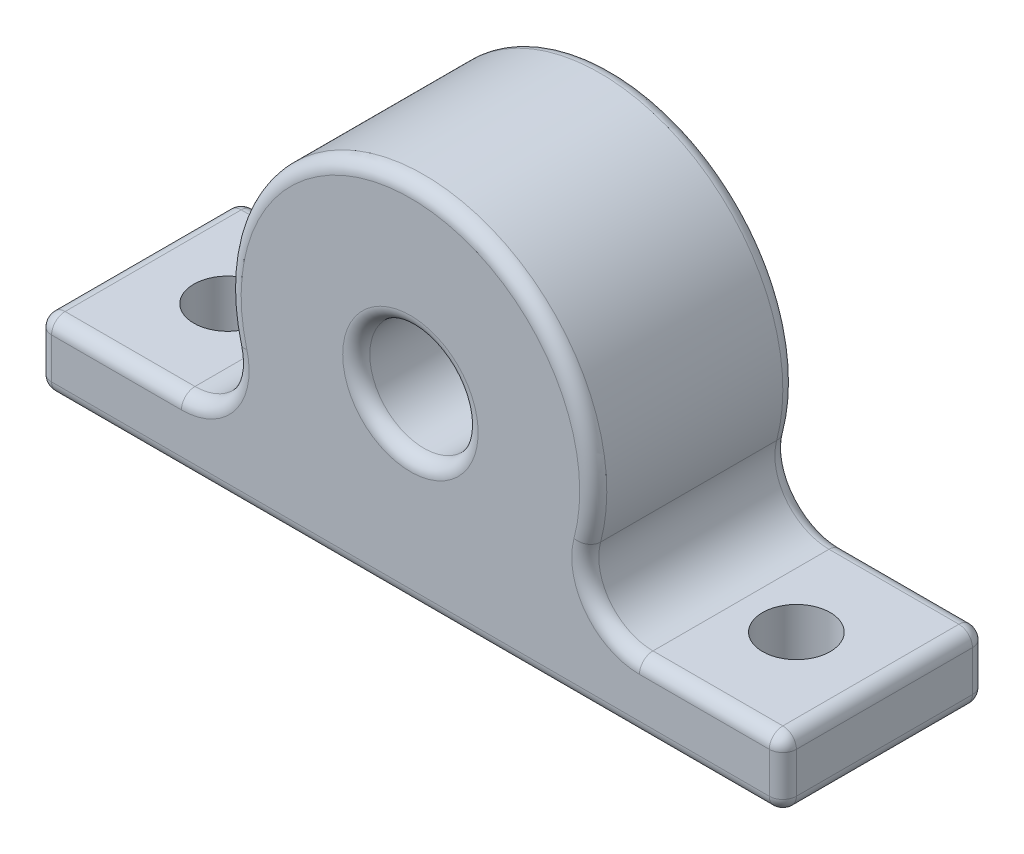
SolidWorks part; units mm, degrees
ref_plane "Piano frontale" through (0, 0, 0) normal (0, 0, 1) x (1, 0, 0)
ref_plane "Piano superiore" through (0, 0, 0) normal (0, 1, 0) x (1, 0, 0)
ref_plane "Piano destro" through (0, 0, 0) normal (1, 0, 0) x (0, 0, -1)
sketch "Schizzo1" plane through (0, 0, 0) normal (0, 1, 0) x (1, 0, 0)
  line L1 (-27.5, 7.5) -> (27.5, 7.5)
  line L2 (-27.5, 7.5) -> (-27.5, -7.5)
  line L3 (-27.5, -7.5) -> (27.5, -7.5)
  line L4 (27.5, 7.5) -> (27.5, -7.5)
  line L5 (-27.5, 7.5) -> (27.5, -7.5) construction
  line L6 (-27.5, -7.5) -> (27.5, 7.5) construction
  point P0 (0, 0)
  dimension "D1" = 15
  dimension "D2" = 55
extrude "Estrusione-Estrusione1" add sketch "Schizzo1" along normal blind 5
sketch "Schizzo2" plane through (0, 0, 0) normal (0, 0, 1) x (1, 0, 0)
  line L1 (5.5, 0) -> (-5.5, 0) construction
  line L2 (0, -5.5) -> (0, 5.5) construction
  circle A0 centre (0, 13.5) radius 13.5
  circle A1 centre (0, 13.5) radius 4
  point P4 (0, 0)
  dimension "D1" = 27
  dimension "D2" = 8
extrude "Estrusione-Estrusione2" add sketch "Schizzo2" along normal up to surface and the other way up to surface up to face at (0, 2.5, 7.5) other way up to face at (0, 2.5, -7.5)
fillet "Raccordo1" radius 4 2 edges at (10.4881, 5, 0) (-10.4881, 5, 0)
fillet "Raccordo2" radius 1 22 edges at (27.5, 5, 0) (27.5, 0, 0) (-27.5, 5, 0) (-27.5, 0, 0) (4, 13.5, -7.5) (-27.5, 2.5, -7.5) (0, 0, -7.5) (27.5, 2.5, -7.5) (22.2058, 5, -7.5) (13.7402, 6.5622, -7.5) (0, 27, -7.5) (-13.7402, 6.5622, -7.5) (-22.2058, 5, -7.5) (-4, 13.5, 7.5) (27.5, 2.5, 7.5) (0, 0, 7.5) (-27.5, 2.5, 7.5) (-22.2058, 5, 7.5) (-13.7402, 6.5622, 7.5) (0, 27, 7.5) (13.7402, 6.5622, 7.5) (22.2058, 5, 7.5)
sketch "Schizzo3" plane through (0, 0, 0) normal (0, 1, 0) x (1, 0, 0)
  line L0 (-23.5, 0) -> (23.5, 0) construction
  line L2 (0, -5.5) -> (0, 5.5) construction
  circle A0 centre (21, 0) radius 2.5
  circle A1 centre (-21, 0) radius 2.5
  point P2 (0, 0)
  dimension "D2" = 5
  dimension "D1" = 47
extrude "Taglio-Estrusione1" cut sketch "Schizzo3" along normal through all
